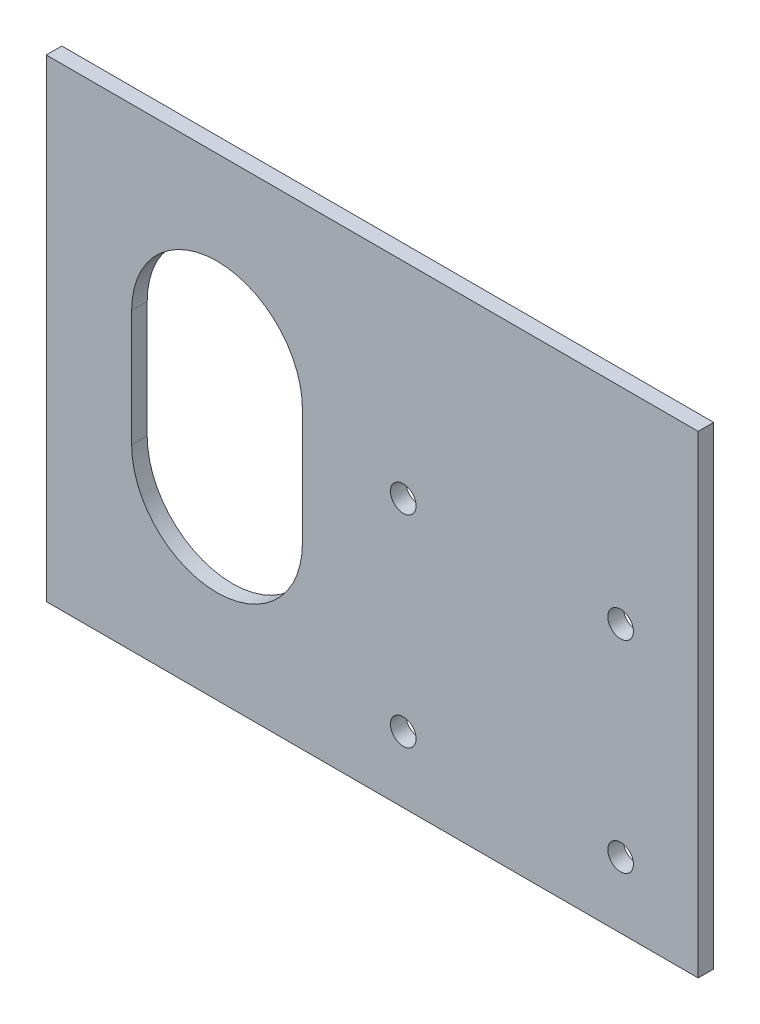
SolidWorks part; units mm, degrees
ref_plane "Front Plane" through (0, 0, 0) normal (0, 0, 1) x (1, 0, 0)
ref_plane "Top Plane" through (0, 0, 0) normal (0, 1, 0) x (1, 0, 0)
ref_plane "Right Plane" through (0, 0, 0) normal (1, 0, 0) x (0, 0, -1)
sketch "Sketch1" plane through (0, 0, 0) normal (0, 0, 1) x (1, 0, 0)
  line L0 (-130.4, 53.2) -> (-130.4, 38.2) construction
  line L1 (-152.4, 76.2) -> (-68.4, 76.2)
  line L2 (-152.4, 76.2) -> (-152.4, 15.2)
  line L3 (-152.4, 15.2) -> (-68.4, 15.2)
  line L4 (-68.4, 76.2) -> (-68.4, 15.2)
  line L5 (-119.4, 53.2) -> (-119.4, 38.2)
  line L6 (-141.4, 53.2) -> (-141.4, 38.2)
  circle A4 centre (-106.4, 23.7) radius 1.65
  circle A5 centre (-78.4, 23.7) radius 1.65
  circle A6 centre (-78.4, 49.7) radius 1.65
  circle A7 centre (-106.4, 49.7) radius 1.65
  arc A8 (-119.4, 53.2) -> (-141.4, 53.2) centre (-130.4, 53.2) ccw
  arc A9 (-141.4, 38.2) -> (-119.4, 38.2) centre (-130.4, 38.2) ccw
  point P19 (-130.4, 45.7)
  point P24 (-131.5938, 55.6105)
  point P25 (-130.5446, 45.2687)
  point P26 (-142.3853, 59.8072)
  point P27 (-129.6453, 52.7628)
  point P28 (0, 0)
  point P29 (-130.3643, 37.87)
  point P30 (0, 0)
  dimension "D4" = 11
  dimension "D1" = 84
  dimension "D2" = 61
  dimension "D3" = 7.5
  dimension "D5" = 30.5
  dimension "D6" = 22
extrude "Boss-Extrude1" add sketch "Sketch1" along normal blind 2
